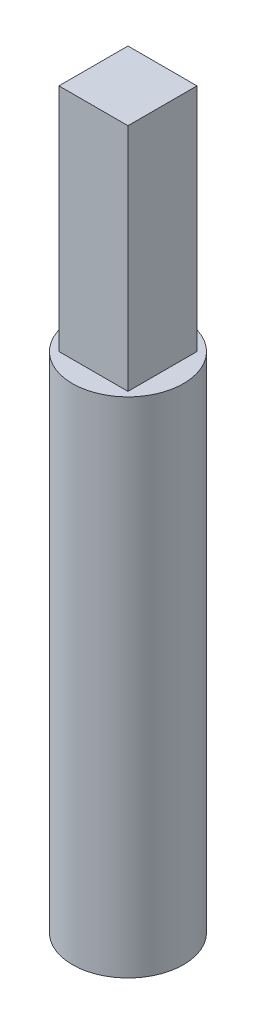
SolidWorks part; units mm, degrees
ref_plane "Front Plane" through (0, 0, 0) normal (0, 0, 1) x (1, 0, 0)
ref_plane "Top Plane" through (0, 0, 0) normal (0, 1, 0) x (1, 0, 0)
ref_plane "Right Plane" through (0, 0, 0) normal (1, 0, 0) x (0, 0, -1)
sketch "Sketch1" plane through (0, 0, 0) normal (0, 1, 0) x (1, 0, 0)
  circle A0 centre (0, 0) radius 3.6805
  dimension "D1" = 7.3609
extrude "Boss-Extrude1" add sketch "Sketch1" along normal blind 33.3375
sketch "Sketch3" plane through (0, 33.3375, 0) normal (0, 1, 0) x (1, 0, 0)
  line L1 (-2.286, 2.286) -> (2.286, 2.286)
  line L2 (-2.286, 2.286) -> (-2.286, -2.286)
  line L3 (-2.286, -2.286) -> (2.286, -2.286)
  line L4 (2.286, 2.286) -> (2.286, -2.286)
  line L5 (-2.286, 2.286) -> (2.286, -2.286) construction
  line L6 (-2.286, -2.286) -> (2.286, 2.286) construction
  point P0 (0, 0)
  dimension "D1" = 4.572
  dimension "D2" = 4.572
extrude "Boss-Extrude2" add sketch "Sketch3" along normal blind 15.24
